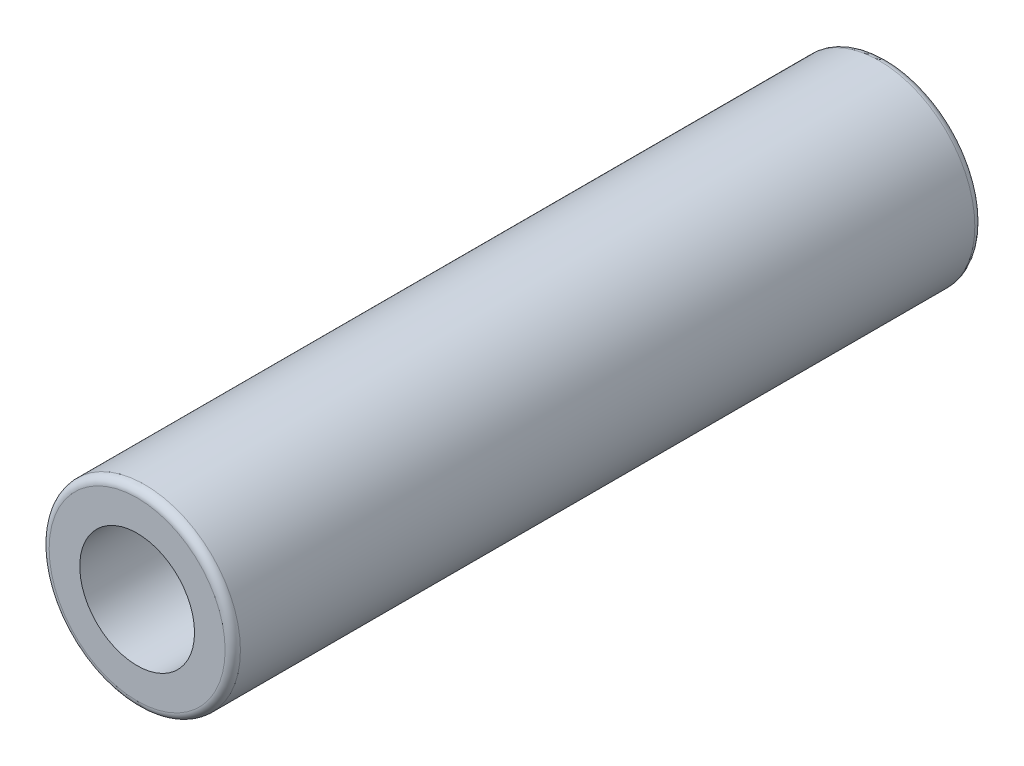
SolidWorks part; units mm, degrees
ref_plane "Front Plane" through (0, 0, 0) normal (0, 0, 1) x (1, 0, 0)
ref_plane "Top Plane" through (0, 0, 0) normal (0, 1, 0) x (1, 0, 0)
ref_plane "Right Plane" through (0, 0, 0) normal (1, 0, 0) x (0, 0, -1)
sketch "Sketch1" plane through (0, 0, 0) normal (0, 0, 1) x (1, 0, 0)
  circle A0 centre (0, 0) radius 6.25
  dimension "D1" = 12.5
extrude "Extrude-Thin2" add sketch "Sketch1" along normal mid plane 49 thin thin type one direction reverse wall 2.5
fillet "Fillet4" radius 0.5 2 edges at (6.25, 0, -24.5) (6.25, 0, 24.5)
